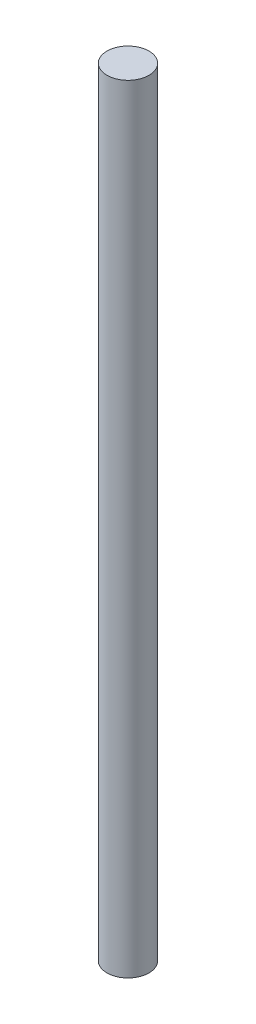
SolidWorks part; units mm, degrees
ref_plane "Front Plane" through (0, 0, 0) normal (0, 0, 1) x (1, 0, 0)
ref_plane "Top Plane" through (0, 0, 0) normal (0, 1, 0) x (1, 0, 0)
ref_plane "Right Plane" through (0, 0, 0) normal (1, 0, 0) x (0, 0, -1)
sketch "Sketch1" plane through (0, 0, 0) normal (0, 1, 0) x (1, 0, 0)
  circle A0 centre (0, 0) radius 0.5
extrude "Boss-Extrude1" add sketch "Sketch1" along normal mid plane 18.5
